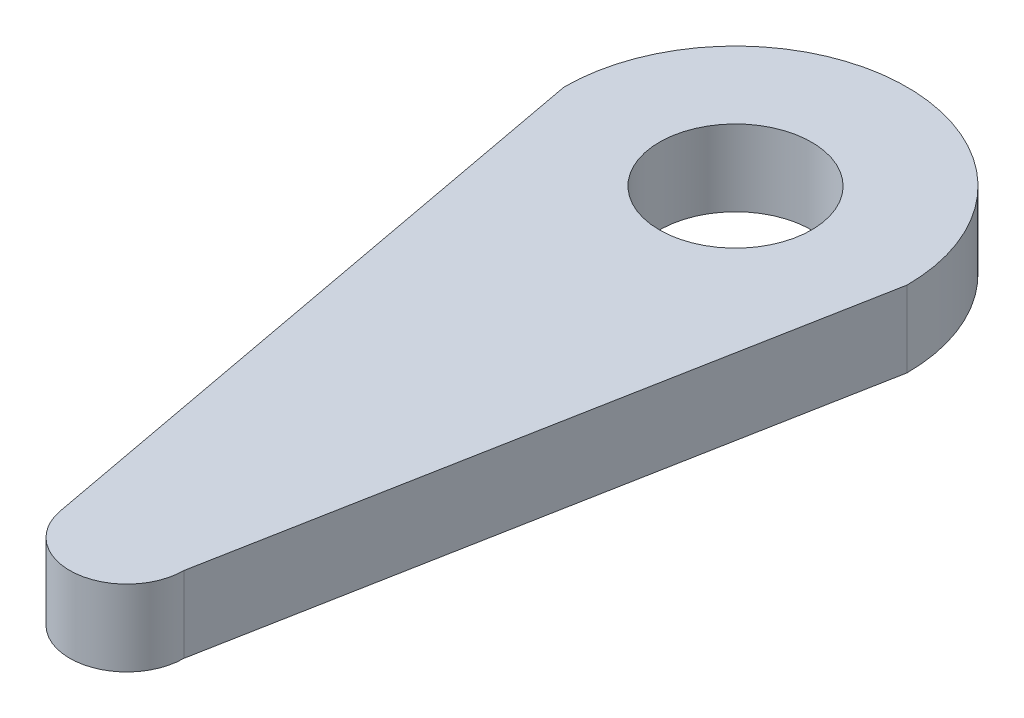
SolidWorks part; units mm, degrees
ref_plane "前视基准面" through (0, 0, 0) normal (0, 0, 1) x (1, 0, 0)
ref_plane "上视基准面" through (0, 0, 0) normal (0, 1, 0) x (1, 0, 0)
ref_plane "右视基准面" through (0, 0, 0) normal (1, 0, 0) x (0, 0, -1)
sketch "草图1" plane through (0, 0, 0) normal (0, 1, 0) x (1, 0, 0)
  line L0 (0, 0) -> (0, -13.4227) construction
  line L1 (-4.5079, 0) -> (-1.4772, -16.2751)
  line L2 (4.5079, 0) -> (1.5026, -16)
  arc A0 (4.5079, 0) -> (-4.5079, 0) centre (0, 0) ccw
  arc A1 (-1.4772, -16.2751) -> (1.5026, -16) centre (0, -16) ccw
  dimension "D1" = 16
extrude "凸台-拉伸1" add sketch "草图1" along normal blind 2
sketch "草图2" plane through (0, 2, 0) normal (0, 1, 0) x (1, 0, 0)
  circle A0 centre (0, 0) radius 2
extrude "切除-拉伸1" cut sketch "草图2" against normal blind 2 contours A0
